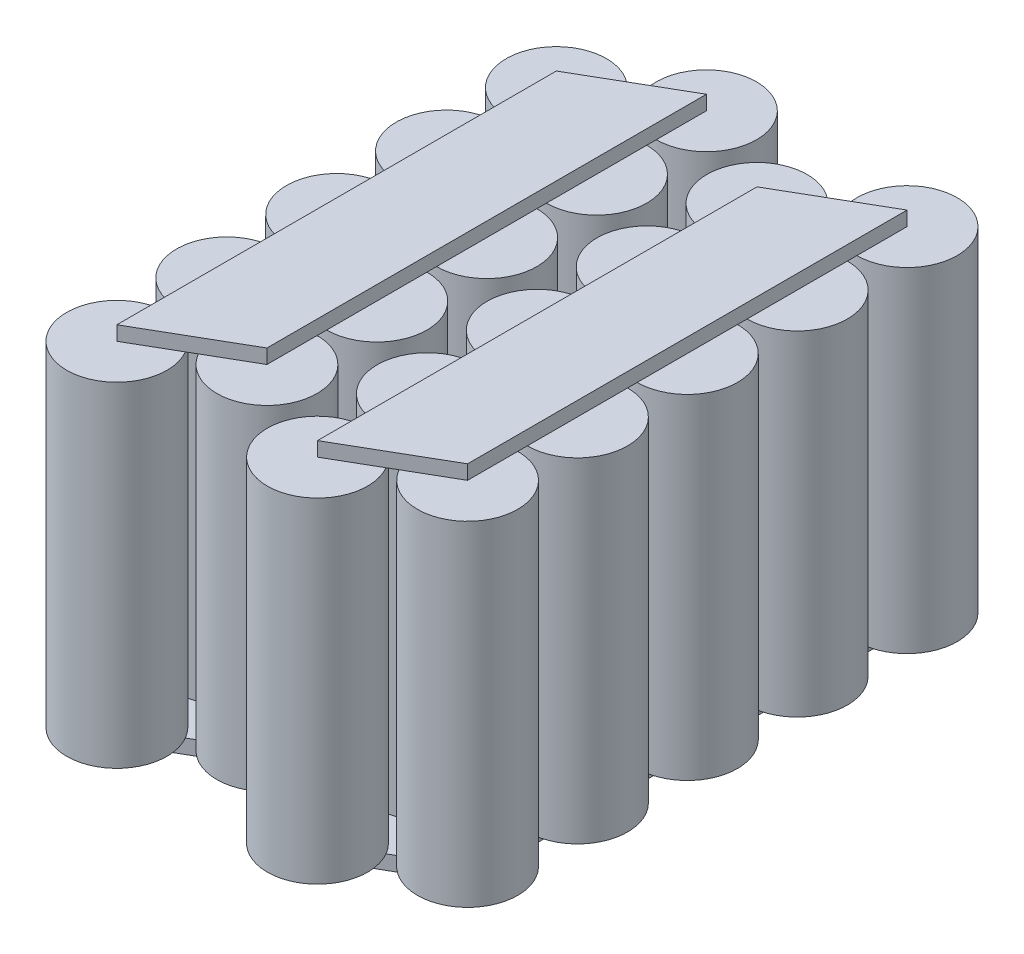
SolidWorks part; units mm, degrees
ref_plane "Front Plane" through (0, 0, 0) normal (0, 0, 1) x (1, 0, 0)
ref_plane "Top Plane" through (0, 0, 0) normal (0, 1, 0) x (1, 0, 0)
ref_plane "Right Plane" through (0, 0, 0) normal (1, 0, 0) x (0, 0, -1)
sketch "Sketch1" plane through (0, 0, 0) normal (0, 1, 0) x (1, 0, 0)
  line L0 (0, 0) -> (0, 24.8473) construction
  line L1 (0, 0) -> (20, 0) construction
  line L2 (0, 0) -> (19.9186, 11.5) construction
  line L4 (0, 0) -> (0, -18.1864) construction
  circle A0 centre (0, 0) radius 10.5
  circle A11 centre (19.9186, 11.5) radius 10.5
  dimension "D1" = 21
  dimension "D2" = 21
  dimension "D3" = 60
  dimension "D4" = 2
extrude "Molicelll 21700 - 4s5p" add sketch "Sketch1" along normal mid plane 70
pattern_linear "LPattern1" count 5 spacing 23 along (0, 0, 1) of "Molicelll 21700 - 4s5p"
pattern_linear "LPattern2" count 2 spacing 42 along (1, 0, 0) of bodies 342 338 341 337 340 336 339 335 334 213
sketch "Sketch2" plane through (0, 35, 0) normal (0, 1, 0) x (1, 0, 0)
  line L0 (0, 0) -> (19.9186, 11.5)
  line L5 (19.9186, 11.5) -> (19.9186, -80.5)
  line L18 (19.9186, -80.5) -> (0, -92)
  line L19 (0, -92) -> (0, 0)
  line L20 (42, 0) -> (61.9186, 11.5)
  line L21 (61.9186, 11.5) -> (61.9186, -80.5)
  line L22 (61.9186, -80.5) -> (42, -92)
  line L23 (42, -92) -> (42, 0)
extrude "Top Bus Bar" add sketch "Sketch2" along normal blind 3 separate body contours L19 L0 L5 L18 | L23 L20 L21 L22
sketch "Sketch3" plane through (0, -35, 0) normal (0, -1, 0) x (1, 0, 0)
  line L0 (0, 92) -> (19.9186, 80.5)
  line L1 (19.9186, 80.5) -> (19.9186, -11.5)
  line L2 (19.9186, -11.5) -> (0, 0)
  line L3 (0, 0) -> (0, 92)
  line L4 (42, 92) -> (61.9186, 80.5)
  line L5 (61.9186, 80.5) -> (61.9186, -11.5)
  line L6 (61.9186, -11.5) -> (42, 0)
  line L7 (42, 0) -> (42, 92)
  circle M9 centre (0, 92) radius 10.5
extrude "Bottom Bus Bar" add sketch "Sketch3" along normal blind 3 separate body contours L3 L2 L1 L0 M9 | L7 L6 L5 L4 | L3 L0 M9
sketch "Sketch5" [suppressed] plane through (0, 0, 0) normal (0, 1, 0) x (1, 0, 0)
  line L0 (-16.5, 28.0001) -> (78.2821, 27.9998)
  line L9 (78.2821, 27.9998) -> (78.5, -108.5)
  line L10 (-16.5, -108.5) -> (78.5, -108.5)
  line L11 (-16.5, 28.0001) -> (-16.5, -108.5)
  circle A9 centre (61.9186, -57.5) radius 10.5 construction
  circle A11 centre (0, -69) radius 10.5 construction
  circle A12 centre (19.9186, 11.5) radius 10.5 construction
  circle A13 centre (42, -92) radius 10.5 construction
  dimension "D3" = 6
  dimension "D5" = 6
  dimension "D6" = 6
  dimension "D1" = 136.5
  dimension "D2" = 95
  dimension "D4" = 6
equation "\"cell_diameter\"= 21"
equation "\"D1@Sketch1\"=\"cell_diameter\""
equation "\"cell_height\"= 70"
equation "\"series\"= 4'number of parllel assem connected in series per stack"
equation "\"parallel\"= 5'number of cells in parallel"
equation "\"lattice\"= 60"
equation "\"s_space\"= 2 * \"cell_diameter\" * cos ( \"lattice\" )"
equation "\"p_space\"= \"cell_diameter\""
equation "\"D1@Molicelll 21700 - 4s5p\" = \"cell_height\""
equation "\"D3@LPattern2\"= \"s_space\""
equation "\"D1@LPattern2\"= \"series\" / 2"
equation "\"D4@LPattern2\"= \"p_space\""
equation "\"D2@LPattern2\"= \"parallel\""
